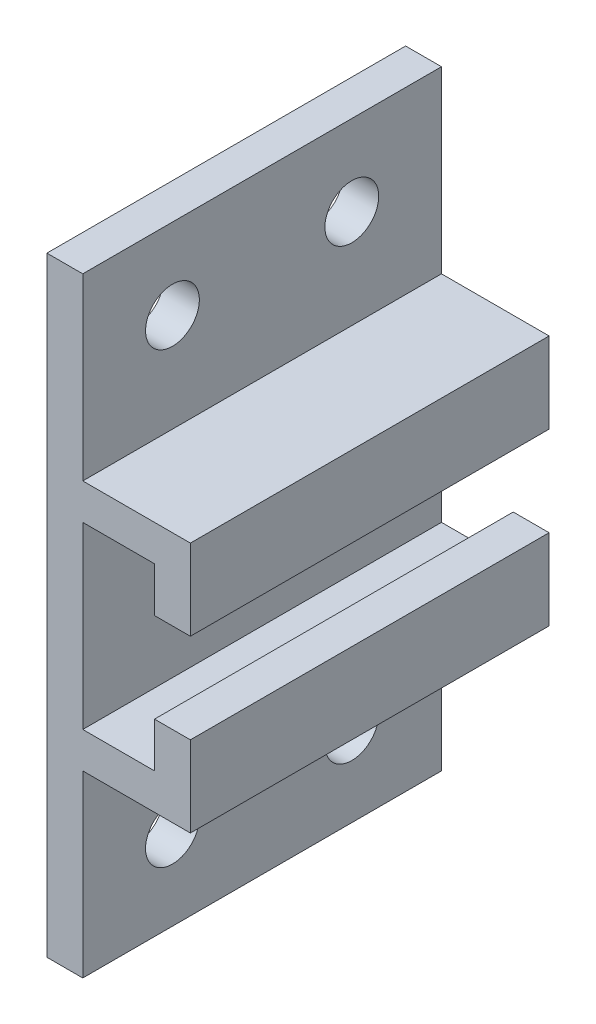
SolidWorks part; units mm, degrees
ref_plane "Front Plane" through (0, 0, 0) normal (0, 0, 1) x (1, 0, 0)
ref_plane "Top Plane" through (0, 0, 0) normal (0, 1, 0) x (1, 0, 0)
ref_plane "Right Plane" through (0, 0, 0) normal (1, 0, 0) x (0, 0, -1)
sketch "Main" plane through (0, 0, 0) normal (0, 0, 1) x (1, 0, 0)
  line L0 (0, 17) -> (0, -17)
  line L1 (0, -17) -> (2, -17)
  line L2 (2, -17) -> (2, -7)
  line L3 (2, -7) -> (8, -7)
  line L4 (8, -7) -> (8, -2.5)
  line L5 (8, -2.5) -> (6, -2.5)
  line L6 (6, -2.5) -> (6, -5)
  line L7 (6, -5) -> (2, -5)
  line L8 (2, -5) -> (2, 5)
  line L9 (2, 5) -> (6, 5)
  line L10 (6, 5) -> (6, 2.5)
  line L11 (6, 2.5) -> (8, 2.5)
  line L12 (8, 2.5) -> (8, 7)
  line L13 (2, 17) -> (2, 7)
  line L14 (0, 17) -> (2, 17)
  line L15 (2, 7) -> (8, 7)
  point P14 (0, 0)
  point P17 (0, 0)
  point P18 (6, -3.75)
  dimension "D1" = 34
  dimension "D2" = 5
  dimension "D3" = 2
  dimension "D4" = 10
  dimension "D5" = 2
  dimension "D7" = 6
  dimension "D8" = 2
  dimension "D9" = 10
extrude "Main Extrusion" add sketch "Main" along normal blind 20
sketch "Wholes" plane through (0, 0, 0) normal (-1, 0, 0) x (0, 0, 1)
  line L0 (20, 17) -> (0, 17) construction
  line L1 (0, 17) -> (0, -17) construction
  line L2 (20, -17) -> (0, -17) construction
  line L3 (20, 17) -> (20, -17) construction
  circle A0 centre (5, 12.5) radius 1.5
  circle A1 centre (5, -12.5) radius 1.5
  circle A2 centre (15, -12.5) radius 1.5
  circle A3 centre (15, 12.5) radius 1.5
  point P14 (16.4817, -15)
  point P15 (4.2089, -15)
  point P16 (0, 0)
  point P17 (16.4817, -15)
  point P20 (0, 0)
  point P21 (0, 0)
  dimension "D1" = 3
  dimension "D2" = 4.5
  dimension "D3" = 5
  dimension "D4" = 4.5
  dimension "D5" = 5
extrude "Whole Removal" cut sketch "Wholes" against normal through all
